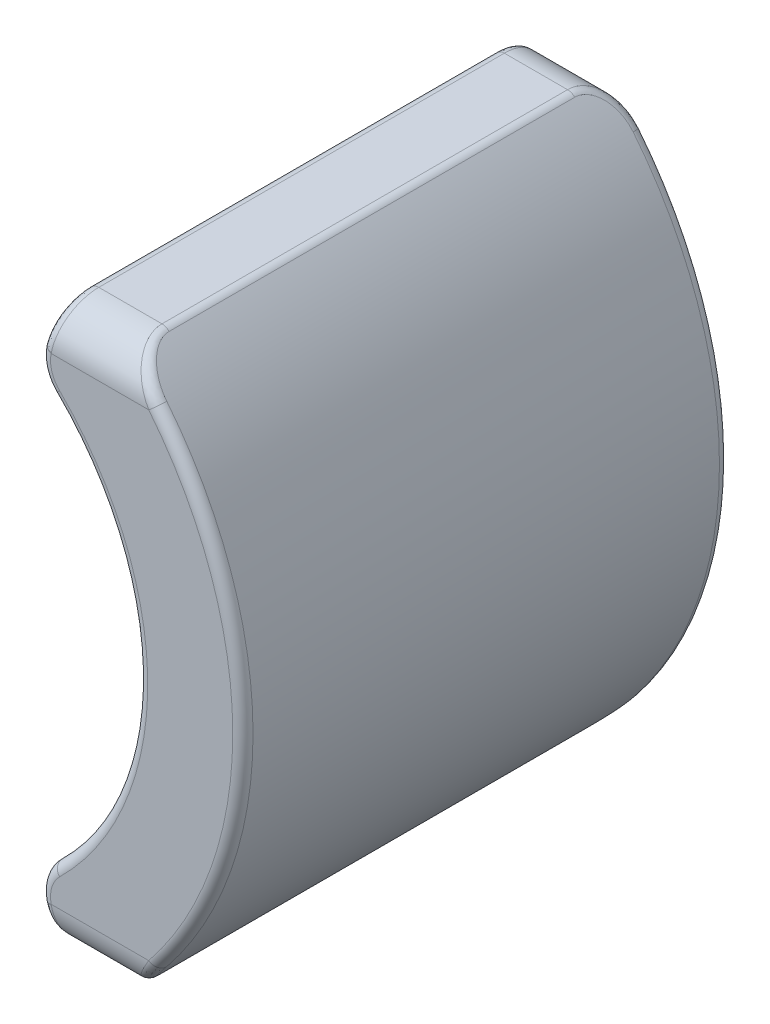
SolidWorks part; units mm, degrees
ref_plane "Front Plane" through (0, 0, 0) normal (0, 0, 1) x (1, 0, 0)
ref_plane "Top Plane" through (0, 0, 0) normal (0, 1, 0) x (1, 0, 0)
ref_plane "Right Plane" through (0, 0, 0) normal (1, 0, 0) x (0, 0, -1)
sketch "Sketch1" plane through (0, 0, 0) normal (0, 0, 1) x (1, 0, 0)
  line L0 (0, 0) -> (8.0158, 0) construction
  line L1 (5.124, -6.88) -> (3.264, -6.88)
  line L2 (3.264, -6.88) -> (2.9177, -5.38)
  line L3 (5.124, 6.88) -> (3.264, 6.88)
  line L4 (3.264, 6.88) -> (2.9177, 5.38)
  arc A0 (5.124, 6.88) -> (5.124, -6.88) centre (-1.6142, 0) cw
  arc A1 (2.9177, 5.38) -> (2.9177, -5.38) centre (-1.6142, 0) cw
  dimension "D1" = 9.63
  dimension "D2" = 6.88
  dimension "D3" = 1.86
  dimension "D4" = 103
  dimension "D5" = 1.5
extrude "Boss-Extrude1" add sketch "Sketch1" along normal blind 12
fillet "Fillet1" radius 1 2 edges at (2.9177, -5.38, 6) (2.9177, 5.38, 6)
fillet "Fillet3" radius 1 1 edges at (4.194, 6.88, 0)
fillet "Fillet4" radius 1 1 edges at (4.194, -6.88, 0)
fillet "Fillet5" radius 1 2 edges at (4.194, 6.88, 12) (4.194, -6.88, 12)
fillet "Fillet6" radius 0.25 24 edges at (3.0737, 5.4113, 0) (3.2019, 6.6112, 0.3178) (3.264, 6.88, 6) (3.2019, 6.6112, 11.6822) (3.0737, 5.4113, 12) (3.0737, -5.4113, 12) (3.2019, -6.6112, 11.6822) (3.264, -6.88, 6) (3.2019, -6.6112, 0.3178) (3.0737, -5.4113, 0) (5.374, 6.6258, 0.3339) (8.0158, 0, 0) (5.2544, -6.7498, 0.5066) (5.124, -6.88, 6) (5.374, -6.6258, 11.6661) (8.0158, 0, 12) (5.2544, 6.7498, 11.4934) (5.124, 6.88, 6) (5.4202, 0, 12) (5.4202, 0, 0)
